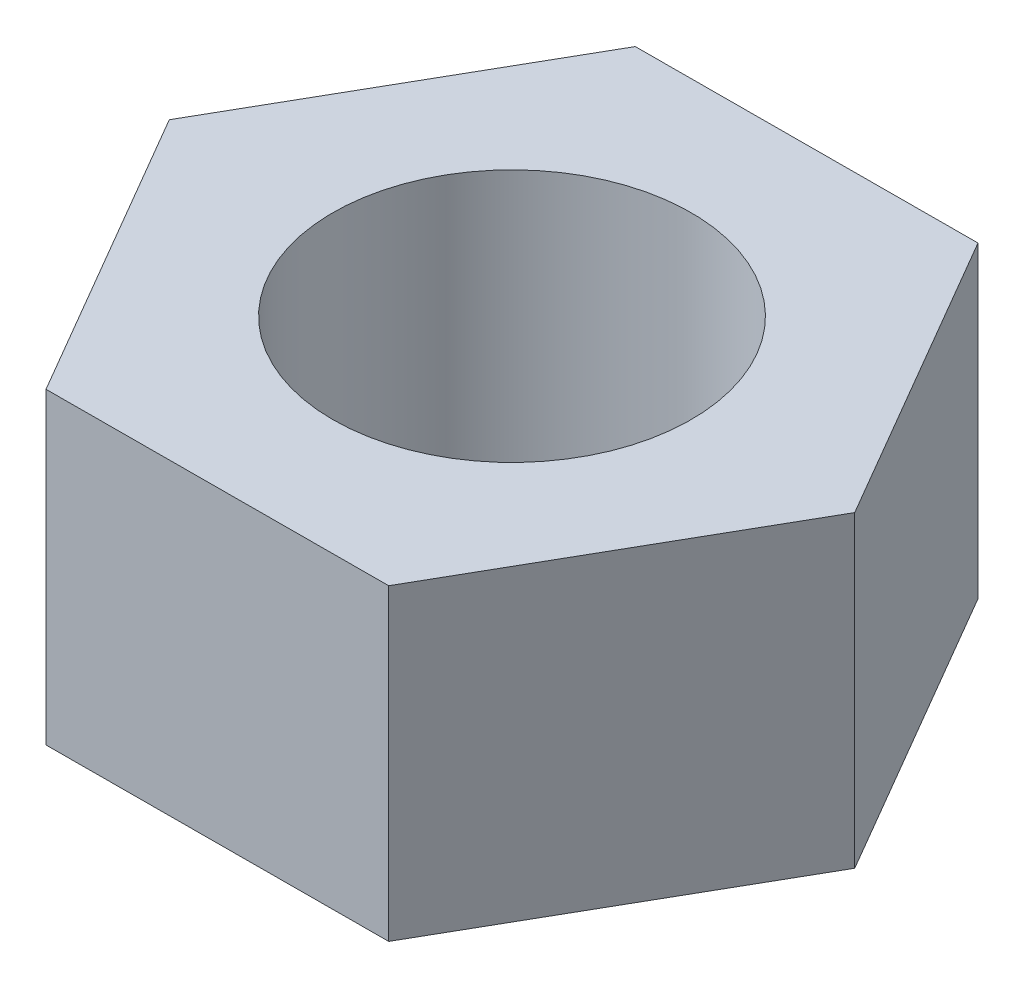
SolidWorks part; units mm, degrees
ref_plane "Front Plane" through (0, 0, 0) normal (0, 0, 1) x (1, 0, 0)
ref_plane "Top Plane" through (0, 0, 0) normal (0, 1, 0) x (1, 0, 0)
ref_plane "Right Plane" through (0, 0, 0) normal (1, 0, 0) x (0, 0, -1)
sketch "Sketch1" plane through (0, 0, 0) normal (0, 1, 0) x (1, 0, 0)
  line L1 (7.6938, 13.4395) -> (-7.792, 13.3828)
  line L2 (-7.792, 13.3828) -> (-15.4858, -0.0567)
  line L3 (-15.4858, -0.0567) -> (-7.6938, -13.4395)
  line L4 (-7.6938, -13.4395) -> (7.792, -13.3828)
  line L5 (7.792, -13.3828) -> (15.4858, 0.0567)
  line L6 (15.4858, 0.0567) -> (7.6938, 13.4395)
  circle A0 centre (0, 0) radius 13.4112 construction
  dimension "D1" = 26.8224
extrude "Boss-Extrude1" add sketch "Sketch1" along normal blind 13.97 contours L1 L2 L3 L4 L5 L6
sketch "Sketch2" plane through (0, 13.97, 0) normal (0, 1, 0) x (1, 0, 0)
  circle A0 centre (0, 0) radius 8.128
extrude "Cut-Extrude1" cut sketch "Sketch2" against normal through all
